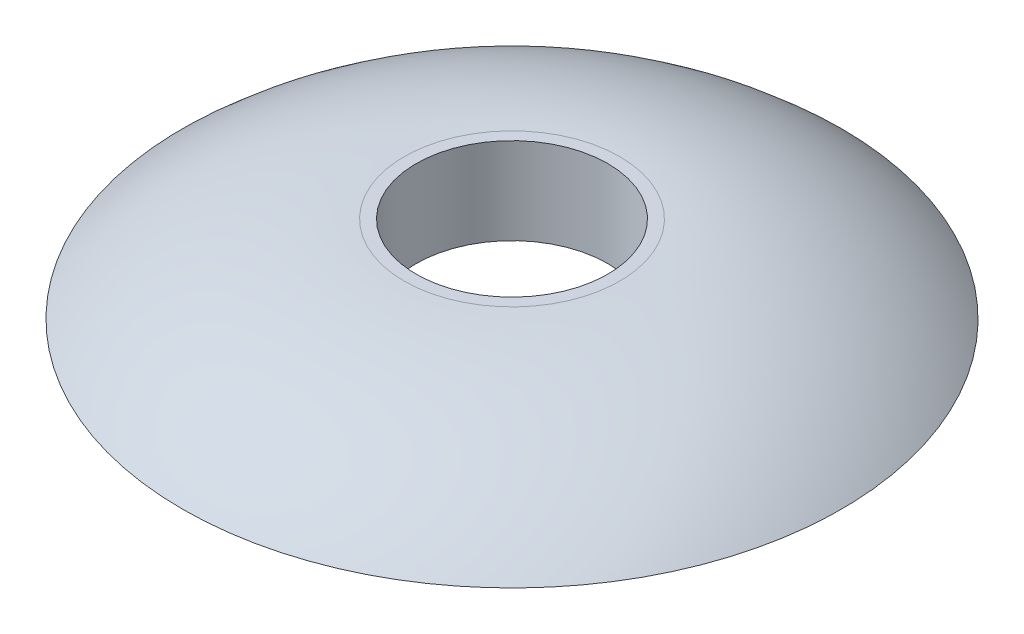
SolidWorks part; units mm, degrees
ref_plane "Front Plane" through (0, 0, 0) normal (0, 0, 1) x (1, 0, 0)
ref_plane "Top Plane" through (0, 0, 0) normal (0, 1, 0) x (1, 0, 0)
ref_plane "Right Plane" through (0, 0, 0) normal (1, 0, 0) x (0, 0, -1)
sketch "Sketch1" plane through (0, 0, 0) normal (0, 0, 1) x (1, 0, 0)
  line L0 (0, 0) -> (-12.7, 0) construction
  line L1 (-12.7, 0) -> (-12.7, 11.4788)
  line L2 (-12.7, 11.4788) -> (-14.2875, 11.4788)
  line L3 (-14.2875, 9.8913) -> (-14.2875, 1.9538)
  line L4 (-14.2875, 1.9538) -> (-37.7337, 1.9538)
  line L6 (-39.6875, 0) -> (-12.7, 0)
  line L8 (-14.2875, 11.4788) -> (-14.2875, 9.8913) construction
  line L9 (0, 0) -> (0, 11.4788) construction
  line L10 (0, 11.4788) -> (-12.7, 11.4788) construction
  line L11 (-43.6718, 0) -> (-41.275, 0)
  line L12 (-39.6875, 0) -> (-37.7337, 1.9538)
  arc A2 (-14.2875, 9.8913) -> (-41.275, 0) centre (-14.2875, -31.8706) ccw
  arc A3 (-14.2875, 11.4788) -> (-43.6718, 0) centre (-14.2875, -31.8706) ccw
  point P4 (-37.7337, 1.9538)
  point P12 (-41.1781, 0)
  dimension "D4" = 7.9375
  dimension "D1" = 12.7
  dimension "D2" = 1.9538
  dimension "D3" = 1.5875
  dimension "D5" = 26.9875
  dimension "D6" = 45
  dimension "D7" = 1.5875
revolve "Revolve1" add sketch "Sketch1" angle 360 about L9
fillet "Fillet1" radius 2.54 1 edges at (0, 1.9538, -14.2875)
